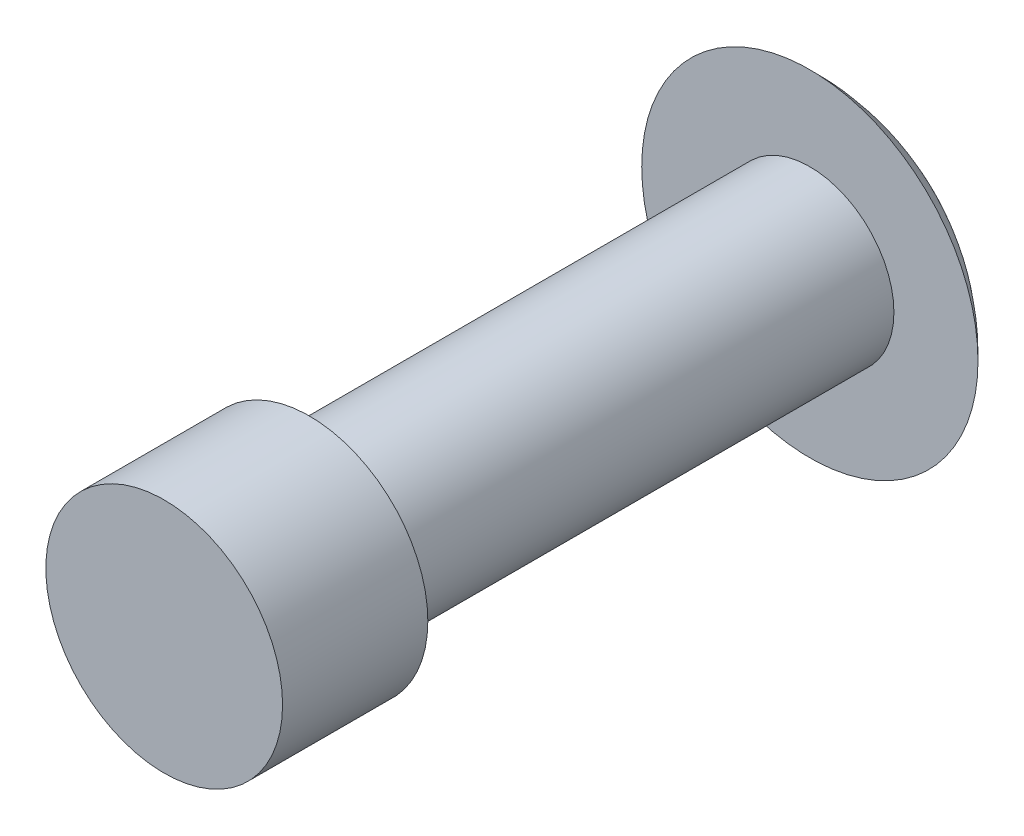
SolidWorks part; units mm, degrees
material "6061 Alloy"
ref_plane "Plane1" through (0, 0, 0) normal (0, 0, 1) x (1, 0, 0)
ref_plane "Plane2" through (0, 0, 0) normal (0, 1, 0) x (1, 0, 0)
ref_plane "Plane3" through (0, 0, 0) normal (1, 0, 0) x (0, 0, -1)
sketch "Sketch1" plane through (0, 0, 0) normal (0, 0, 1) x (1, 0, 0)
  circle A0 centre (0, 0) radius 1.9844
  dimension "Diameter" = 3.9688
extrude "Base-Extrude" add sketch "Sketch1" along normal blind 15.24
sketch "Sketch2" plane through (0, 0, 0) normal (0, 1, 0) x (1, 0, 0)
  line L2 (0, -15.24) -> (0, 0) construction
  line L3 (0, 1.7018) -> (0, 0)
  line L4 (0, 0) -> (3.9688, 0)
  line L5 (3.9688, 0) -> (-3.9688, 0) construction
  line L6 (-3.9688, 0) -> (-3.9688, 9.6833) construction
  line L7 (0, 0) -> (0, 24.2412) construction
  arc A0 (0, 1.7018) -> (3.9688, 0) centre (0, -3.7768) cw
  dimension "Head Dia" = 7.9375
  dimension "Head Thick" = 1.7018
revolve "Boss-Revolve1" add sketch "Sketch2" angle 360 about L7
sketch "Sketch3" plane through (0, 0, 15.24) normal (0, 0, 1) x (1, 0, 0)
  circle A0 centre (0, 0) radius 2.794
  dimension "D1" = 5.588
extrude "Extrude1" add sketch "Sketch3" against normal offset from surface (3.429 mm away) 11.811 up to face at (3.9688, 0, 0)
fillet "Fillet1" [suppressed] radius 0.127
